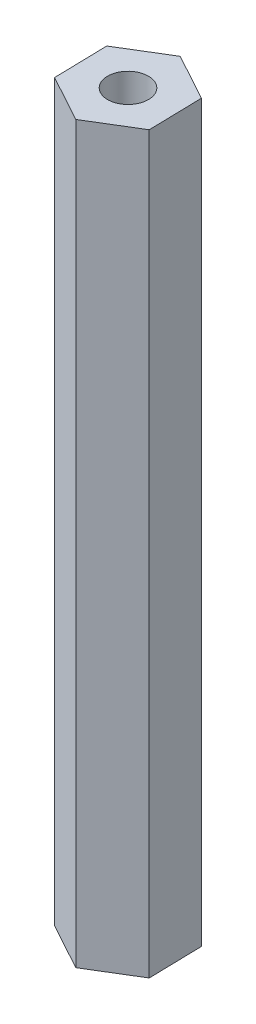
SolidWorks part; units mm, degrees
ref_plane "Front Plane" through (0, 0, 0) normal (0, 0, 1) x (1, 0, 0)
ref_plane "Top Plane" through (0, 0, 0) normal (0, 1, 0) x (1, 0, 0)
ref_plane "Right Plane" through (0, 0, 0) normal (1, 0, 0) x (0, 0, -1)
sketch "Sketch1" plane through (0, 0, 0) normal (0, 1, 0) x (1, 0, 0)
  line L1 (3.1567, 1.9215) -> (-0.0857, 3.6945)
  line L2 (-0.0857, 3.6945) -> (-3.2424, 1.773)
  line L3 (-3.2424, 1.773) -> (-3.1567, -1.9215)
  line L4 (-3.1567, -1.9215) -> (0.0857, -3.6945)
  line L5 (0.0857, -3.6945) -> (3.2424, -1.773)
  line L6 (3.2424, -1.773) -> (3.1567, 1.9215)
  circle A0 centre (0, 0) radius 3.2004 construction
  dimension "D1" = 6.4008
extrude "Boss-Extrude1" add sketch "Sketch1" along normal blind 50.8
hole_wizard "#34 (0.111) Diameter Hole1" positions "Sketch3" profile "Sketch4" hole size "#34" standard "ANSI Inch" end condition through all
sketch "Sketch3" plane through (0, 0, 0) normal (0, -1, 0) x (-1, 0, 0)
  point P0 (0, 0)
sketch "Sketch4" plane through (0, 0, 0) normal (1, 0, 0) x (0, 0, -1)
  line L0 (0, 0) -> (0, 50.8)
  line L1 (0, 50.8) -> (1.4097, 50.8)
  line L2 (1.4097, 50.8) -> (1.4097, 0)
  line L5 (1.4097, 0) -> (0, 0)
  line L11 (0, -6.35) -> (0, 107.95) construction
  dimension "Thru Hole Dia." = 2.8194
  dimension "Thru Hole Depth" = 50.8
